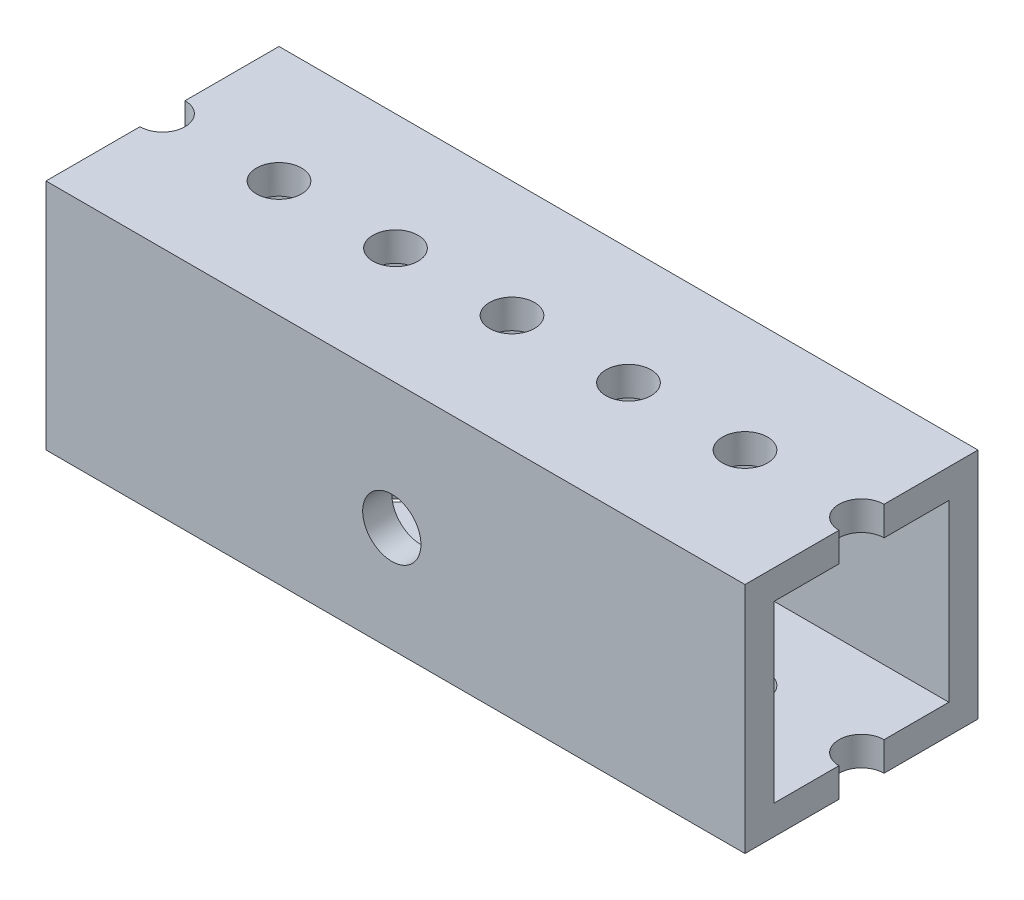
SolidWorks part; units mm, degrees
material "6061 Alloy"
ref_plane "Front Plane" through (0, 0, 0) normal (0, 0, 1) x (1, 0, 0)
ref_plane "Top Plane" through (0, 0, 0) normal (0, 1, 0) x (1, 0, 0)
ref_plane "Right Plane" through (0, 0, 0) normal (1, 0, 0) x (0, 0, -1)
sketch "Sketch1" plane through (0, 0, 0) normal (1, 0, 0) x (0, 0, -1)
  line L1 (-9.525, -9.525) -> (9.525, -9.525)
  line L2 (-9.525, -9.525) -> (-9.525, 9.525)
  line L3 (-9.525, 9.525) -> (9.525, 9.525)
  line L4 (9.525, -9.525) -> (9.525, 9.525)
  line L5 (-9.525, -9.525) -> (9.525, 9.525) construction
  line L6 (-9.525, 9.525) -> (9.525, -9.525) construction
  line L7 (-12.7, -12.7) -> (12.7, -12.7)
  line L8 (-12.7, -12.7) -> (-12.7, 12.7)
  line L9 (-12.7, 12.7) -> (12.7, 12.7)
  line L10 (12.7, -12.7) -> (12.7, 12.7)
  line L11 (-12.7, -12.7) -> (12.7, 12.7) construction
  line L12 (-12.7, 12.7) -> (12.7, -12.7) construction
  point P0 (0, 0)
  point P6 (0, 0)
  dimension "D1" = 25.4
  dimension "D2" = 3.175
extrude "Base Tube" add sketch "Sketch1" along normal mid plane 76.2
sketch "Sketch2" plane through (0, 12.7, 0) normal (0, 1, 0) x (1, 0, 0)
  line L0 (0, 12.7) -> (0, -12.7) construction
  line L1 (38.1, 12.7) -> (-38.1, 12.7) construction
  line L2 (38.1, -12.7) -> (-38.1, -12.7) construction
  point P9 (0, 0)
hole_wizard "Initial #10 Hole" positions "Sketch2" profile "Sketch4" hole size "#10" standard "ANSI Inch" end condition through all
sketch "Sketch4" plane through (0, 12.7, 0) normal (1, 0, 0) x (0, 0, 1)
  line L0 (0, 0) -> (0, 25.4)
  line L1 (0, 25.4) -> (2.4574, 25.4)
  line L2 (2.4574, 25.4) -> (2.4574, 0)
  line L5 (2.4574, 0) -> (0, 0)
  line L11 (0, -6.35) -> (0, 107.95) construction
  dimension "Thru Hole Dia." = 4.9149
  dimension "Thru Hole Depth" = 25.4
pattern_linear "#10 Hole Pattern" count 4 spacing 12.7 along (1, 0, 0) count 4 spacing 12.7 along (-1, 0, 0) of "Initial #10 Hole"
sketch "Sketch5" [suppressed] plane through (0, 12.7, 0) normal (0, 1, 0) x (1, 0, 0)
  line L0 (107.95, -12.7) -> (107.95, 12.7) construction
  line L1 (107.95, 0) -> (95.25, 0) construction
  circle A0 centre (95.25, 0) radius 7.62
  dimension "D2" = 15.24
  dimension "D1" = 12.7
extrude "Intake Shaft Hole" [suppressed] cut sketch "Sketch5" against normal through all
sketch "Sketch6" [suppressed] plane through (0, 0, 12.7) normal (0, 0, 1) x (1, 0, 0)
  line L0 (-241.3, 0) -> (-228.6, 0) construction
  line L1 (-241.3, 12.7) -> (-241.3, -12.7) construction
  line L2 (241.3, 0) -> (228.6, 0) construction
  line L3 (241.3, 12.7) -> (241.3, -12.7) construction
  point P1 (-228.6, 0)
  point P6 (228.6, 0)
  dimension "D1" = 12.7
hole_wizard "Front Mounting Bolt" [suppressed] positions "Sketch6" profile "Sketch7" hole size "#10" standard "ANSI Inch"
sketch "Sketch7" [suppressed] plane through (228.6, 0, 12.7) normal (1, 0, 0) x (0, -1, 0)
  line L0 (0, 0) -> (0, 26.8766)
  line L1 (0, 26.8766) -> (2.4574, 25.4)
  line L2 (2.4574, 25.4) -> (2.4574, 0)
  line L5 (2.4574, 0) -> (0, 0)
  line L10 (0, 26.8766) -> (-2.4574, 25.4) construction
  line L11 (0, -6.35) -> (0, 107.95) construction
  dimension "Hole Dia." = 4.9149
  dimension "Hole Depth" = 25.4
  dimension "Drill Angle" = 118
sketch "Sketch8" plane through (0, 0, 12.7) normal (0, 0, 1) x (1, 0, 0)
  circle A0 centre (-0.4025, -1.1951) radius 3.175
  dimension "D1" = 6.35
extrude "Cut-Extrude1" cut sketch "Sketch8" against normal up to next
